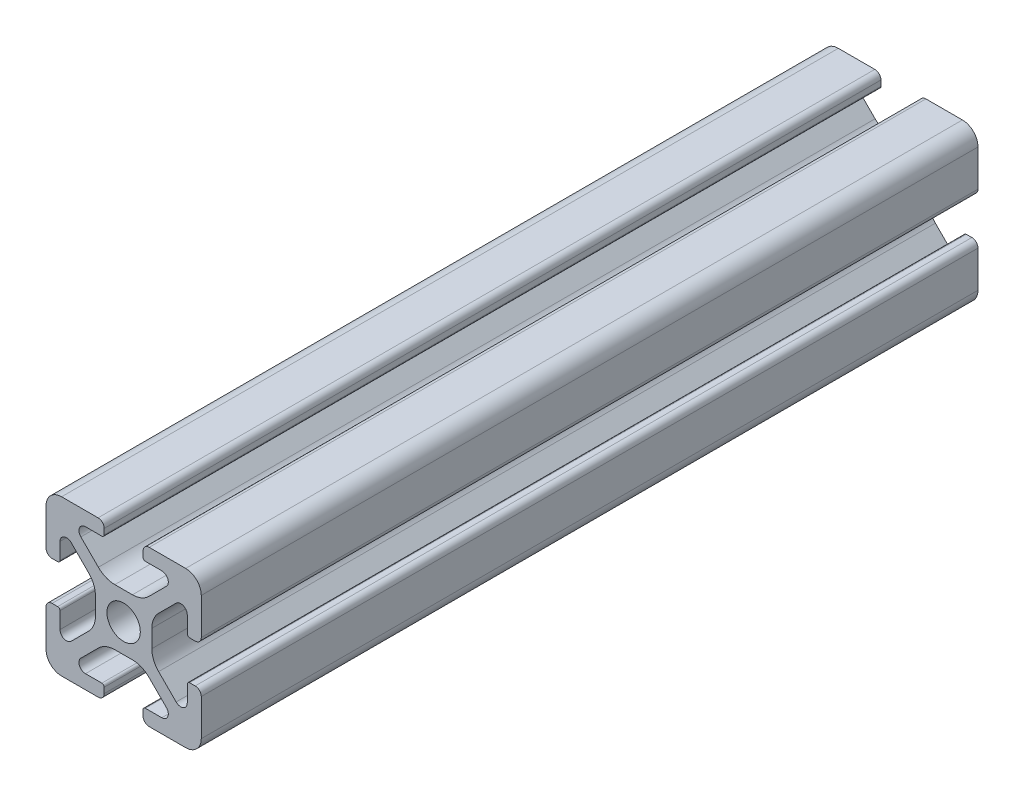
SolidWorks part; units mm, degrees
ref_plane "Front Plane" through (0, 0, 0) normal (0, 0, 1) x (1, 0, 0)
ref_plane "Top Plane" through (0, 0, 0) normal (0, 1, 0) x (1, 0, 0)
ref_plane "Right Plane" through (0, 0, 0) normal (1, 0, 0) x (0, 0, -1)
sketch "Sketch1" plane through (0, 0, 0) normal (0, 0, 1) x (1, 0, 0)
  line L2 (-9.9949, 7.9883) -> (-9.9949, 3.2893)
  line L3 (-7.9883, 9.9949) -> (-3.2893, 9.9949)
  line L4 (-2.5019, 9.2075) -> (-2.5019, 8.4963)
  line L5 (-2.8067, 8.1915) -> (-4.9149, 8.1915)
  line L6 (-5.5076, 6.7606) -> (-3.2528, 4.5058)
  line L7 (-6.7606, 5.5076) -> (-4.5058, 3.2528)
  line L8 (-8.1915, 4.9149) -> (-8.1915, 2.8067)
  line L9 (-8.4963, 2.5019) -> (-9.2075, 2.5019)
  line L11 (-1.1334, 3.6279) -> (1.1334, 3.6279)
  line L12 (-3.6279, 1.1334) -> (-3.6279, -1.1334)
  line L13 (8.4963, 2.5019) -> (9.2075, 2.5019)
  line L14 (8.1915, 4.9149) -> (8.1915, 2.8067)
  line L15 (9.9949, 7.9883) -> (9.9949, 3.2893)
  line L16 (7.9883, 9.9949) -> (3.2893, 9.9949)
  line L17 (2.5019, 9.2075) -> (2.5019, 8.4963)
  line L18 (2.8067, 8.1915) -> (4.9149, 8.1915)
  line L19 (3.6279, 1.1334) -> (3.6279, -1.1334)
  line L20 (5.5076, 6.7606) -> (3.2528, 4.5058)
  line L21 (6.7606, 5.5076) -> (4.5058, 3.2528)
  line L22 (-8.4963, -2.5019) -> (-9.2075, -2.5019)
  line L23 (-8.1915, -4.9149) -> (-8.1915, -2.8067)
  line L24 (-6.7606, -5.5076) -> (-4.5058, -3.2528)
  line L25 (-5.5076, -6.7606) -> (-3.2528, -4.5058)
  line L26 (-2.8067, -8.1915) -> (-4.9149, -8.1915)
  line L27 (-2.5019, -9.2075) -> (-2.5019, -8.4963)
  line L28 (-7.9883, -9.9949) -> (-3.2893, -9.9949)
  line L29 (-9.9949, -7.9883) -> (-9.9949, -3.2893)
  line L30 (9.9949, -7.9883) -> (9.9949, -3.2893)
  line L31 (7.9883, -9.9949) -> (3.2893, -9.9949)
  line L32 (2.5019, -9.2075) -> (2.5019, -8.4963)
  line L33 (2.8067, -8.1915) -> (4.9149, -8.1915)
  line L34 (5.5076, -6.7606) -> (3.2528, -4.5058)
  line L35 (6.7606, -5.5076) -> (4.5058, -3.2528)
  line L36 (8.1915, -4.9149) -> (8.1915, -2.8067)
  line L37 (8.4963, -2.5019) -> (9.2075, -2.5019)
  line L38 (-1.1334, -3.6279) -> (1.1334, -3.6279)
  circle A0 centre (0, 0) radius 2.1463
  arc A1 (-9.9949, 7.9883) -> (-7.9883, 9.9949) centre (-7.9883, 7.9883) cw
  arc A2 (-6.7606, 5.5076) -> (-8.1915, 4.9149) centre (-7.3533, 4.9149) ccw
  arc A3 (-4.9149, 8.1915) -> (-5.5076, 6.7606) centre (-4.9149, 7.3533) ccw
  arc A4 (-3.2893, 9.9949) -> (-2.5019, 9.2075) centre (-3.2893, 9.2075) cw
  arc A5 (-9.9949, 3.2893) -> (-9.2075, 2.5019) centre (-9.2075, 3.2893) ccw
  arc A6 (-8.1915, 2.8067) -> (-8.4963, 2.5019) centre (-8.4963, 2.8067) cw
  arc A7 (-2.5019, 8.4963) -> (-2.8067, 8.1915) centre (-2.8067, 8.4963) cw
  arc A8 (-1.1334, 3.6279) -> (-3.2528, 4.5058) centre (-1.1334, 6.6251) cw
  arc A9 (-3.6279, 1.1334) -> (-4.5058, 3.2528) centre (-6.6251, 1.1334) ccw
  arc A10 (8.1915, 2.8067) -> (8.4963, 2.5019) centre (8.4963, 2.8067) ccw
  arc A11 (9.9949, 3.2893) -> (9.2075, 2.5019) centre (9.2075, 3.2893) cw
  arc A12 (9.9949, 7.9883) -> (7.9883, 9.9949) centre (7.9883, 7.9883) ccw
  arc A13 (3.2893, 9.9949) -> (2.5019, 9.2075) centre (3.2893, 9.2075) ccw
  arc A14 (2.5019, 8.4963) -> (2.8067, 8.1915) centre (2.8067, 8.4963) ccw
  arc A15 (1.1334, 3.6279) -> (3.2528, 4.5058) centre (1.1334, 6.6251) ccw
  arc A16 (3.6279, 1.1334) -> (4.5058, 3.2528) centre (6.6251, 1.1334) cw
  arc A17 (6.7606, 5.5076) -> (8.1915, 4.9149) centre (7.3533, 4.9149) cw
  arc A18 (4.9149, 8.1915) -> (5.5076, 6.7606) centre (4.9149, 7.3533) cw
  arc A19 (-3.6279, -1.1334) -> (-4.5058, -3.2528) centre (-6.6251, -1.1334) cw
  arc A20 (-1.1334, -3.6279) -> (-3.2528, -4.5058) centre (-1.1334, -6.6251) ccw
  arc A21 (-2.5019, -8.4963) -> (-2.8067, -8.1915) centre (-2.8067, -8.4963) ccw
  arc A22 (-8.1915, -2.8067) -> (-8.4963, -2.5019) centre (-8.4963, -2.8067) ccw
  arc A23 (-9.9949, -3.2893) -> (-9.2075, -2.5019) centre (-9.2075, -3.2893) cw
  arc A24 (-3.2893, -9.9949) -> (-2.5019, -9.2075) centre (-3.2893, -9.2075) ccw
  arc A25 (-4.9149, -8.1915) -> (-5.5076, -6.7606) centre (-4.9149, -7.3533) cw
  arc A26 (-6.7606, -5.5076) -> (-8.1915, -4.9149) centre (-7.3533, -4.9149) cw
  arc A27 (-9.9949, -7.9883) -> (-7.9883, -9.9949) centre (-7.9883, -7.9883) ccw
  arc A28 (9.9949, -7.9883) -> (7.9883, -9.9949) centre (7.9883, -7.9883) cw
  arc A29 (6.7606, -5.5076) -> (8.1915, -4.9149) centre (7.3533, -4.9149) ccw
  arc A30 (4.9149, -8.1915) -> (5.5076, -6.7606) centre (4.9149, -7.3533) ccw
  arc A31 (3.2893, -9.9949) -> (2.5019, -9.2075) centre (3.2893, -9.2075) cw
  arc A32 (9.9949, -3.2893) -> (9.2075, -2.5019) centre (9.2075, -3.2893) ccw
  arc A33 (8.1915, -2.8067) -> (8.4963, -2.5019) centre (8.4963, -2.8067) cw
  arc A34 (2.5019, -8.4963) -> (2.8067, -8.1915) centre (2.8067, -8.4963) cw
  arc A35 (1.1334, -3.6279) -> (3.2528, -4.5058) centre (1.1334, -6.6251) cw
  arc A36 (3.6279, -1.1334) -> (4.5058, -3.2528) centre (6.6251, -1.1334) ccw
extrude "Boss-Extrude1" add sketch "Sketch1" along normal mid plane 100
